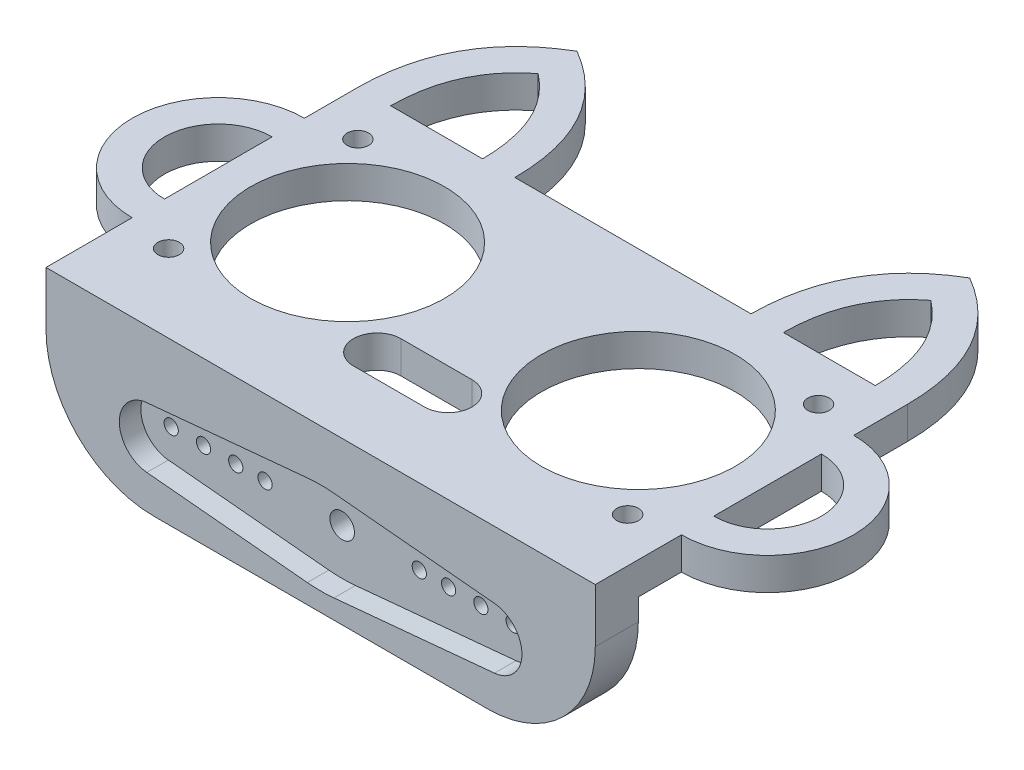
SolidWorks part; units mm, degrees
ref_plane "Front Plane" through (0, 0, 0) normal (0, 0, 1) x (1, 0, 0)
ref_plane "Top Plane" through (0, 0, 0) normal (0, 1, 0) x (1, 0, 0)
ref_plane "Right Plane" through (0, 0, 0) normal (1, 0, 0) x (0, 0, -1)
sketch "Sketch1" plane through (0, 0, 0) normal (0, 1, 0) x (1, 0, 0)
  line L0 (-25.5, -13) -> (25.5, -13)
  line L1 (25.5, 13) -> (25.5, 8)
  line L2 (-10.9649, 13) -> (10.9649, 13)
  line L3 (-25.5, 13) -> (-25.5, 8)
  line L8 (0, 13) -> (0, 18.5944) construction
  line L9 (-25.5, 5) -> (-25.5, -5)
  line L10 (-25.5, -8) -> (-25.5, -13)
  line L11 (25.5, 5) -> (25.5, -5)
  line L12 (25.5, 5) -> (25.5, -5)
  line L13 (25.5, -8) -> (25.5, -13)
  line L14 (-13.965, 13) -> (-22.4999, 13)
  line L15 (13.965, 13) -> (22.4999, 13)
  line L16 (25.5, 0) -> (-25.5, 0) construction
  line L17 (21.3692, 8.8641) -> (-21.3307, -8.789) construction
  line L18 (-3.3, -5.25) -> (3.3, -5.25)
  line L19 (3.3, -9.65) -> (-3.3, -9.65)
  circle A0 centre (-13.5, 0) radius 9
  circle A1 centre (13.5, 0) radius 9
  arc A6 (-25.5, 5) -> (-25.5, -5) centre (-25.5, 0) ccw
  arc A7 (-25.5, 8) -> (-25.5, -8) centre (-25.5, 0) ccw
  circle A8 centre (-25.5, 0) radius 8 construction
  circle A9 centre (-25.5, 0) radius 5 construction
  arc A10 (25.5, 5) -> (25.5, -5) centre (25.5, 0) cw
  arc A11 (25.5, 8) -> (25.5, -8) centre (25.5, 0) cw
  circle A12 centre (-21.3307, -8.789) radius 1
  circle A13 centre (21.3692, 8.8641) radius 1
  circle A14 centre (-21.3307, 8.789) radius 1
  circle A15 centre (21.3692, -8.8641) radius 1
  arc A16 (-3.3, -9.65) -> (-5.5, -7.45) centre (-3.3, -7.45) cw
  arc A17 (-5.5, -7.45) -> (-3.3, -5.25) centre (-3.3, -7.45) cw
  arc A18 (3.3, -5.25) -> (5.5, -7.45) centre (3.3, -7.45) cw
  arc A19 (5.5, -7.45) -> (3.3, -9.65) centre (3.3, -7.45) cw
  spline S0 degree 2 poles (-25.5, 13) (-25.448, 21.8306) (-18.2325, 26.0373) knots 0 0 0 1 1 1
  spline S1 degree 2 poles (-10.9649, 13) (-11.017, 21.8306) (-18.2325, 26.0373) knots 0 0 0 1 1 1
  spline S2 degree 2 poles (25.5, 13) (25.448, 21.8306) (18.2325, 26.0373) knots 0 0 0 1 1 1
  spline S3 degree 2 poles (10.9649, 13) (11.017, 21.8306) (18.2325, 26.0373) knots 0 0 0 1 1 1
  spline S6 degree 3 poles (-22.5001, 12.9823) (-22.4985, 13.2504) (-22.4832, 13.7945) (-22.4064, 14.8171) (-22.2257, 16.0183) (-21.8813, 17.3293) (-21.26, 18.9229) (-20.3946, 20.3189) (-19.2677, 21.5635) (-18.5832, 22.1583) (-18.2325, 22.4304) knots 0 0 0 0 0.053955 0.10791 0.21582 0.32373 0.43164 0.64746 0.75537 0.86328 0.86328 0.86328 0.86328
  spline S7 degree 3 poles (-18.2325, 22.4304) (-17.8818, 22.1583) (-17.1972, 21.5635) (-16.0703, 20.3189) (-15.205, 18.9229) (-14.5836, 17.3293) (-14.2392, 16.0183) (-14.0585, 14.8171) (-13.9817, 13.7945) (-13.9665, 13.2504) (-13.9649, 12.9823) knots 0 0 0 0 0.10791 0.21582 0.43164 0.53955 0.64746 0.75537 0.809325 0.86328 0.86328 0.86328 0.86328
  spline S10 degree 3 poles (13.9649, 12.9823) (13.9665, 13.2504) (13.9817, 13.7945) (14.0585, 14.8171) (14.2392, 16.0183) (14.5836, 17.3293) (15.205, 18.9229) (16.0703, 20.3189) (17.1972, 21.5635) (17.8818, 22.1583) (18.2325, 22.4304) knots 0 0 0 0 0.053955 0.10791 0.21582 0.32373 0.43164 0.64746 0.75537 0.86328 0.86328 0.86328 0.86328
  spline S11 degree 3 poles (18.2325, 22.4304) (18.5832, 22.1583) (19.2677, 21.5635) (20.3946, 20.3189) (21.26, 18.9229) (21.8813, 17.3293) (22.2257, 16.0183) (22.4064, 14.8171) (22.4832, 13.7945) (22.4985, 13.2504) (22.5001, 12.9823) knots 0 0 0 0 0.10791 0.21582 0.43164 0.53955 0.64746 0.75537 0.809325 0.86328 0.86328 0.86328 0.86328
  dimension "D1" = 18
  dimension "D2" = 18
  dimension "D3" = 10
  dimension "D4" = 3
extrude "Boss-Extrude3" add sketch "Sketch1" along normal blind 3
sketch "Sketch4" plane through (0, 3, 0) normal (0, 1, 0) x (1, 0, 0)
  line L0 (25.5, -8) -> (25.5, -13) construction
  line L2 (-25.5, -13) -> (-25.5, -16)
  line L3 (-25.5, -16) -> (25.5, -16)
  line L4 (25.5, -13) -> (25.5, -16)
  line L7 (-25.5, -13) -> (-25.5, -12)
  line L8 (-25.5, -12) -> (25.5, -12)
  line L9 (25.5, -13) -> (25.5, -12)
  dimension "D1" = 3
  dimension "D2" = 1
extrude "Boss-Extrude4" add sketch "Sketch4" against normal blind 15
sketch "Sketch5" plane through (0, 0, 12) normal (0, 0, -1) x (-1, 0, 0)
  line L0 (-16.5354, -6) -> (16.5354, -6) construction
  line L1 (0, 0) -> (0, -12) construction
  line L2 (-25.5, -12) -> (25.5, -12) construction
  line L3 (0, -6) -> (-25.5, -6) construction
  line L4 (-25.5, -12) -> (-25.5, 0) construction
  line L5 (0, -6) -> (-13.5659, -6) construction
  circle A0 centre (-15.875, -6) radius 0.6604
  circle A1 centre (-12.8778, -6) radius 0.6604
  circle A2 centre (-9.8806, -6) radius 0.6604
  circle A3 centre (-7.1628, -6) radius 0.6604
  circle A4 centre (15.875, -6) radius 0.6604
  circle A5 centre (12.8778, -6) radius 0.6604
  circle A6 centre (9.8806, -6) radius 0.6604
  circle A7 centre (7.1628, -6) radius 0.6604
  circle A8 centre (0, -6) radius 1.143
extrude "Cut-Extrude1" cut sketch "Sketch5" against normal blind 10
fillet "Fillet2" radius 10 2 edges at (-25.5, -12, 14) (25.5, -12, 14)
sketch "Sketch7" plane through (0, 0, 16) normal (0, 0, 1) x (1, 0, 0)
  line L0 (1.1905, -9.7106) -> (16.0923, -8.3075) construction
  line L1 (-1.1905, -9.7106) -> (-16.0923, -8.3075) construction
  line L2 (-1.1905, -2.2894) -> (-16.0923, -3.6925) construction
  line L3 (1.1905, -2.2894) -> (16.0923, -3.6925) construction
  line L4 (15.875, -6) -> (-15.875, -6) construction
  line L5 (0, -12) -> (0, -6) construction
  line L6 (-15.5, -12) -> (15.5, -12) construction
  line L7 (1.2374, -10.2084) -> (16.1391, -8.8053)
  line L8 (1.2374, -1.7916) -> (16.1391, -3.1947)
  line L9 (-1.2374, -1.7916) -> (-16.1391, -3.1947)
  line L10 (-1.2374, -10.2084) -> (-16.1391, -8.8053)
  arc A0 (16.0923, -8.3075) -> (16.0923, -3.6925) centre (15.875, -6) ccw construction
  arc A1 (-1.1905, -9.7106) -> (1.1905, -9.7106) centre (0, 2.9335) ccw construction
  arc A2 (-16.0923, -3.6925) -> (-16.0923, -8.3075) centre (-15.875, -6) ccw construction
  arc A3 (1.1905, -2.2894) -> (-1.1905, -2.2894) centre (0, -14.9335) ccw construction
  arc A4 (16.1391, -8.8053) -> (16.1391, -3.1947) centre (15.875, -6) ccw
  arc A5 (1.2374, -1.7916) -> (-1.2374, -1.7916) centre (0, -14.9335) ccw
  arc A6 (-16.1391, -3.1947) -> (-16.1391, -8.8053) centre (-15.875, -6) ccw
  arc A7 (-1.2374, -10.2084) -> (1.2374, -10.2084) centre (0, 2.9335) ccw
  dimension "D1" = 0.5
extrude "Cut-Extrude3" cut sketch "Sketch7" against normal blind 2
sketch "Sketch8" plane through (0, 0, 0) normal (0, -1, 0) x (1, 0, 0)
  line L0 (22.5, 0) -> (-22.5, 0) construction
  line L1 (5.38, -8.7) -> (-5.38, -8.7) construction
  line L2 (4.58, -7.5) -> (4.58, -9.9) construction
  line L3 (3.04, -9.9) -> (4.58, -9.9) construction
  line L4 (3.04, -7.5) -> (3.04, -9.9) construction
  line L5 (3.04, -7.5) -> (4.58, -7.5) construction
  line L6 (-4.58, -7.5) -> (-4.58, -9.9) construction
  line L7 (-4.58, -9.9) -> (-3.04, -9.9) construction
  line L8 (-3.04, -9.9) -> (-3.04, -7.5) construction
  line L9 (-3.04, -7.5) -> (-4.58, -7.5) construction
  line L10 (5.38, -6.7) -> (5.38, -10.7)
  line L11 (5.38, -10.7) -> (-5.38, -10.7)
  line L12 (5.38, -6.7) -> (-5.38, -6.7)
  line L13 (0, 0) -> (0, -8.7) construction
  line L14 (-5.38, -6.7) -> (-5.38, -10.7)
extrude "Cut-Extrude4" cut sketch "Sketch8" against normal blind 1.3
